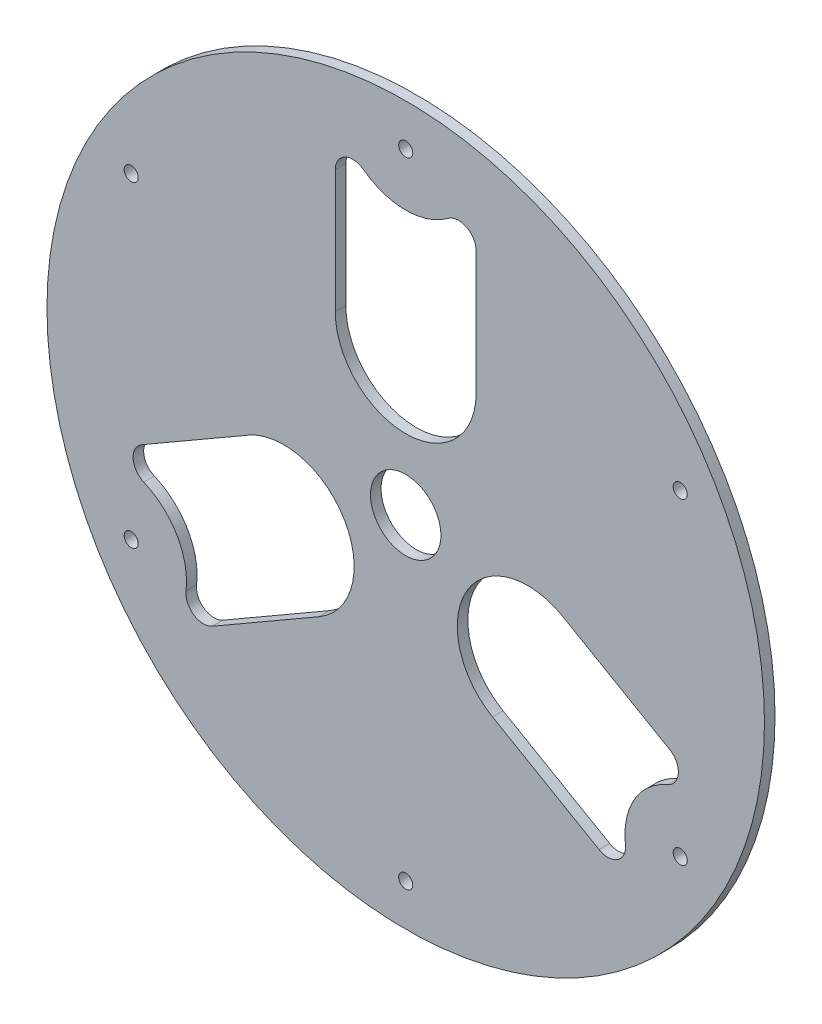
SolidWorks part; units mm, degrees
ref_plane "Front Plane" through (0, 0, 0) normal (0, 0, 1) x (1, 0, 0)
ref_plane "Top Plane" through (0, 0, 0) normal (0, 1, 0) x (1, 0, 0)
ref_plane "Right Plane" through (0, 0, 0) normal (1, 0, 0) x (0, 0, -1)
sketch "Sketch1" plane through (0, 0, 0) normal (0, 0, 1) x (1, 0, 0)
  line L0 (-20, 74.9551) -> (-20, 40)
  line L1 (20, 74.9551) -> (20, 40)
  line L2 (74.913, -20.157) -> (44.641, -2.6795)
  line L3 (54.913, -54.7981) -> (24.641, -37.3205)
  line L4 (-54.913, -54.7981) -> (-24.641, -37.3205)
  line L5 (-74.913, -20.157) -> (-44.641, -2.6795)
  circle A0 centre (0, 0) radius 101.8592
  arc A1 (-20, 40) -> (20, 40) centre (0, 40) ccw
  circle A2 centre (0, 90) radius 2
  arc A3 (-12, 78.9551) -> (12, 78.9551) centre (0, 94.9551) ccw
  arc A4 (-12, 78.9551) -> (-20, 74.9551) centre (-15, 74.9551) ccw
  arc A5 (20, 74.9551) -> (12, 78.9551) centre (15, 74.9551) ccw
  arc A6 (44.641, -2.6795) -> (24.641, -37.3205) centre (34.641, -20) ccw
  arc A7 (74.3771, -29.0852) -> (62.3771, -49.8698) centre (82.2335, -47.4775) ccw
  arc A8 (74.3771, -29.0852) -> (74.913, -20.157) centre (72.413, -24.4872) ccw
  arc A9 (54.913, -54.7981) -> (62.3771, -49.8698) centre (57.413, -50.4679) ccw
  arc A10 (-24.641, -37.3205) -> (-44.641, -2.6795) centre (-34.641, -20) ccw
  arc A11 (-62.3771, -49.8698) -> (-74.3771, -29.0852) centre (-82.2335, -47.4775) ccw
  arc A12 (-62.3771, -49.8698) -> (-54.913, -54.7981) centre (-57.413, -50.4679) ccw
  arc A13 (-74.913, -20.157) -> (-74.3771, -29.0852) centre (-72.413, -24.4872) ccw
  circle A14 centre (77.9423, 45) radius 2
  circle A15 centre (77.9423, -45) radius 2
  circle A16 centre (0, -90) radius 2
  circle A17 centre (-77.9423, -45) radius 2
  circle A18 centre (-77.9423, 45) radius 2
  circle A19 centre (0, 0) radius 10
  point P38 (0, 0)
  point P49 (0, 0)
  dimension "D1" = 203.7183
  dimension "D2" = 40
  dimension "D4" = 4
  dimension "D5" = 10
  dimension "D6" = 10
  dimension "D10" = 20
  dimension "D3" = 40
  dimension "D7" = 90
  dimension "D8" = 3
  dimension "D9" = 6
extrude "Boss-Extrude1" add sketch "Sketch1" along normal blind 3
